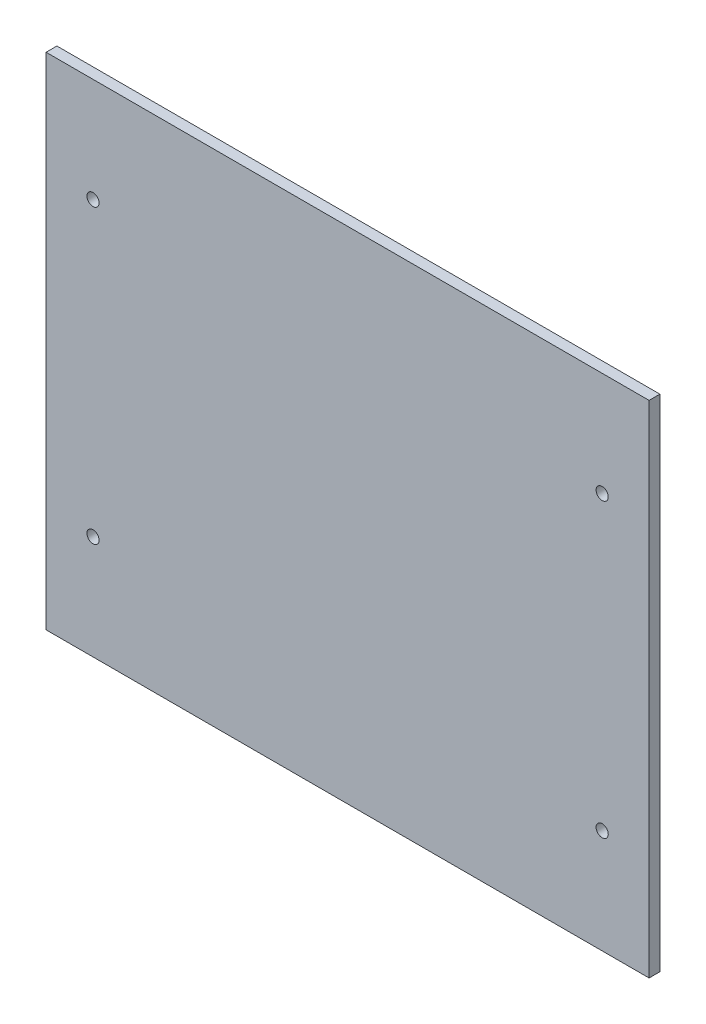
SolidWorks part; units mm, degrees
ref_plane "Front Plane" through (0, 0, 0) normal (0, 0, 1) x (1, 0, 0)
ref_plane "Top Plane" through (0, 0, 0) normal (0, 1, 0) x (1, 0, 0)
ref_plane "Right Plane" through (0, 0, 0) normal (1, 0, 0) x (0, 0, -1)
sketch "Sketch1" plane through (0, 0, 0) normal (0, 0, 1) x (1, 0, 0)
  line L1 (111.5, 92.5) -> (-111.5, 92.5)
  line L2 (111.5, 92.5) -> (111.5, -92.5)
  line L3 (111.5, -92.5) -> (-111.5, -92.5)
  line L4 (-111.5, 92.5) -> (-111.5, -92.5)
  line L5 (111.5, 92.5) -> (-111.5, -92.5) construction
  line L6 (111.5, -92.5) -> (-111.5, 92.5) construction
  circle A0 centre (94.15, -54) radius 2 construction
  circle A1 centre (94.15, 54) radius 2 construction
  circle A2 centre (-94.15, 54) radius 2 construction
  circle A3 centre (-94.15, -54) radius 2 construction
  circle A4 centre (94.15, -54) radius 2
  circle A5 centre (94.15, 54) radius 2
  circle A6 centre (-94.15, 54) radius 2
  circle A7 centre (-94.15, -54) radius 2
  circle A8 centre (-94.15, 54) radius 2.25
  circle A9 centre (94.15, 54) radius 2.25
  circle A10 centre (94.15, -54) radius 2.25
  circle A11 centre (-94.15, -54) radius 2.25
  point P12 (0, 0)
  dimension "D3" = 4.5
  dimension "D1" = 223
  dimension "D2" = 185
extrude "Boss-Extrude1" add sketch "Sketch1" along normal blind 4 contours L1 L4 L3 L2 A11 A10 A9 A8
